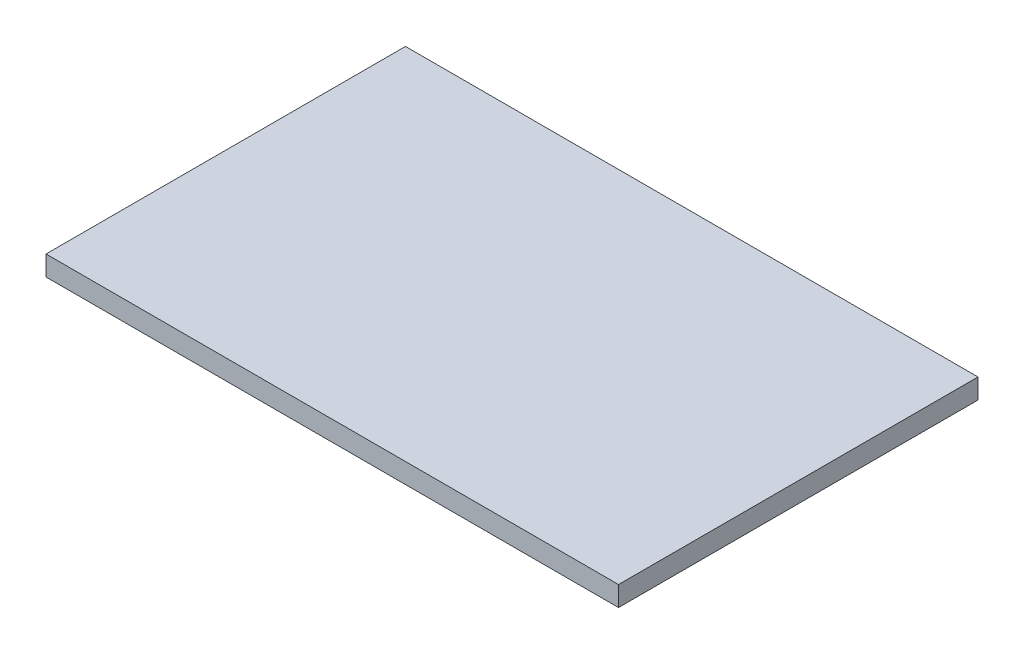
SolidWorks part; units mm, degrees
ref_plane "Plano frontal" through (0, 0, 0) normal (0, 0, 1) x (1, 0, 0)
ref_plane "Plano superior" through (0, 0, 0) normal (0, 1, 0) x (1, 0, 0)
ref_plane "Plano direito" through (0, 0, 0) normal (1, 0, 0) x (0, 0, -1)
sketch "Esboço1" plane through (0, 0, 0) normal (0, 0, 1) x (1, 0, 0)
  line L1 (0, 0) -> (4300, 0)
  line L2 (0, 0) -> (0, 150)
  line L3 (0, 150) -> (4300, 150)
  line L4 (4300, 0) -> (4300, 150)
  dimension "D1" = 150
  dimension "D2" = 4300
extrude "Ressalto-extrusão1" add sketch "Esboço1" along normal blind 2700
